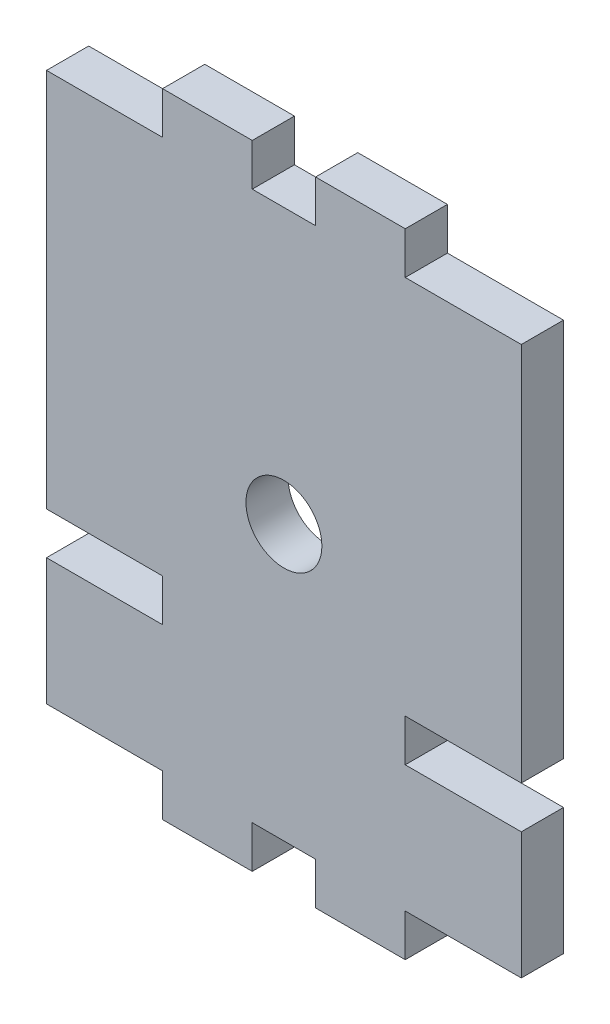
SolidWorks part; units mm, degrees
ref_plane "Front Plane" through (0, 0, 0) normal (0, 0, 1) x (1, 0, 0)
ref_plane "Top Plane" through (0, 0, 0) normal (0, 1, 0) x (1, 0, 0)
ref_plane "Right Plane" through (0, 0, 0) normal (1, 0, 0) x (0, 0, -1)
sketch "Sketch1" plane through (0, 0, 0) normal (0, 0, 1) x (1, 0, 0)
  line L1 (0, 0) -> (45, 0)
  line L2 (0, 0) -> (0, 60)
  line L3 (0, 60) -> (45, 60)
  line L4 (45, 0) -> (45, 60)
  line L10 (0, 30) -> (45, 30) construction
  line L19 (11, 0) -> (11, 4)
  line L34 (0, 60) -> (11, 60)
  line L35 (0, 60) -> (0, 56)
  line L36 (0, 56) -> (11, 56)
  line L37 (11, 60) -> (11, 56)
  line L38 (19.5, 60) -> (25.5, 60)
  line L39 (19.5, 60) -> (19.5, 56)
  line L40 (19.5, 56) -> (25.5, 56)
  line L41 (25.5, 60) -> (25.5, 56)
  line L42 (45, 60) -> (34, 60)
  line L43 (45, 60) -> (45, 56)
  line L44 (45, 56) -> (34, 56)
  line L45 (34, 60) -> (34, 56)
  line L46 (0, 4) -> (11, 4)
  line L47 (0, 0) -> (0, 4)
  line L48 (0, 0) -> (11, 0)
  line L49 (34, 0) -> (34, 4)
  line L50 (45, 4) -> (34, 4)
  line L51 (45, 0) -> (45, 4)
  line L52 (45, 0) -> (34, 0)
  line L53 (25.5, 0) -> (25.5, 4)
  line L54 (19.5, 4) -> (25.5, 4)
  line L55 (19.5, 0) -> (19.5, 4)
  line L56 (19.5, 0) -> (25.5, 0)
  line L58 (0, 20) -> (11, 20)
  line L59 (0, 20) -> (0, 16)
  line L60 (0, 16) -> (11, 16)
  line L61 (11, 20) -> (11, 16)
  line L62 (45, 20) -> (34, 20)
  line L63 (45, 20) -> (45, 16)
  line L64 (45, 16) -> (34, 16)
  line L65 (34, 20) -> (34, 16)
  circle A1 centre (22.5, 30) radius 3.6
  point P8 (22.5, 30)
  point P10 (45, 30)
  point P11 (22.5, 60)
  point P18 (0, 58)
  point P26 (22.5, 56)
  dimension "D3" = 16
  dimension "D4" = 7.2
  dimension "D1" = 45
  dimension "D2" = 60
  dimension "D6" = 11
  dimension "D7" = 4
  dimension "D8" = 6
  dimension "D9" = 11
extrude "Boss-Extrude1" add sketch "Sketch1" along normal blind 4
